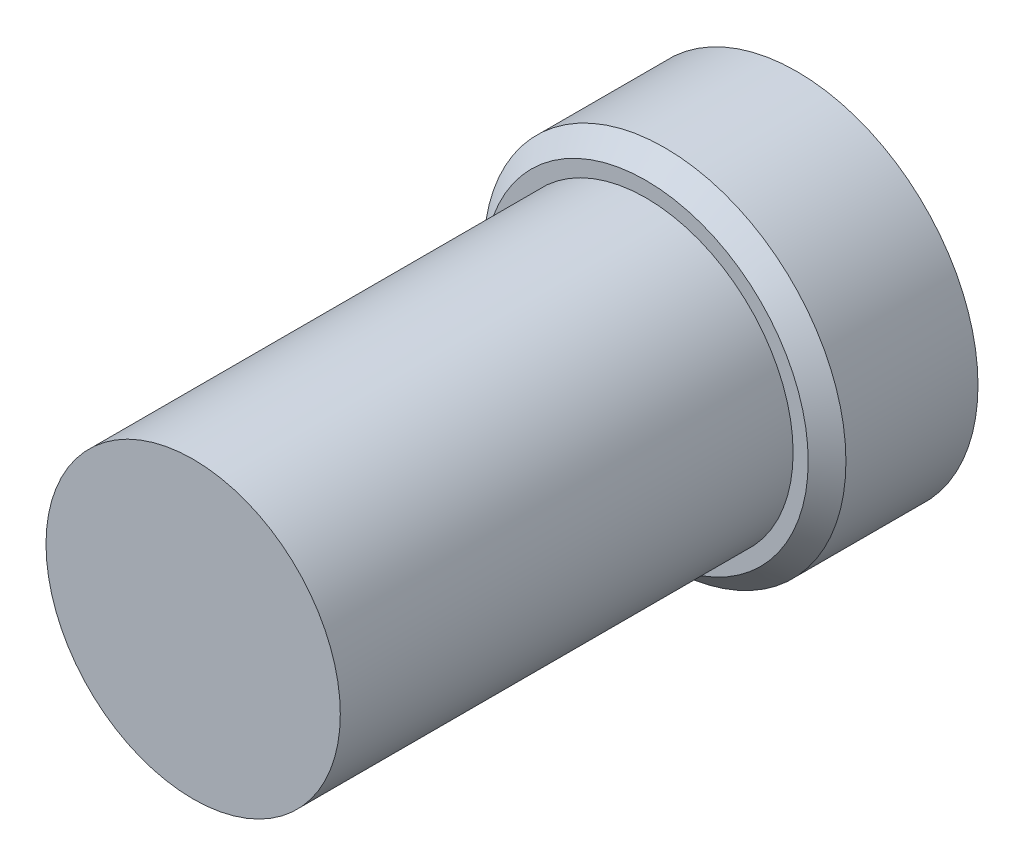
SolidWorks part; units mm, degrees
material "黄铜"
ref_plane "前视基准面" through (0, 0, 0) normal (0, 0, 1) x (1, 0, 0)
ref_plane "上视基准面" through (0, 0, 0) normal (0, 1, 0) x (1, 0, 0)
ref_plane "右视基准面" through (0, 0, 0) normal (1, 0, 0) x (0, 0, -1)
sketch "草图1" plane through (0, 0, 0) normal (0, 0, 1) x (1, 0, 0)
  circle A0 centre (0, 0) radius 2.4
  dimension "D1" = 4.8
extrude "拉伸1" add sketch "草图1" along normal blind 2
sketch "草图2" plane through (0, 0, 2) normal (0, 0, 1) x (1, 0, 0)
  circle A0 centre (0, 0) radius 1.95
  dimension "D1" = 3.9
extrude "拉伸2" add sketch "草图2" along normal blind 6
chamfer "倒角1" distance 0.25 angle 45 1 edges at (2.4, 0, 2)
